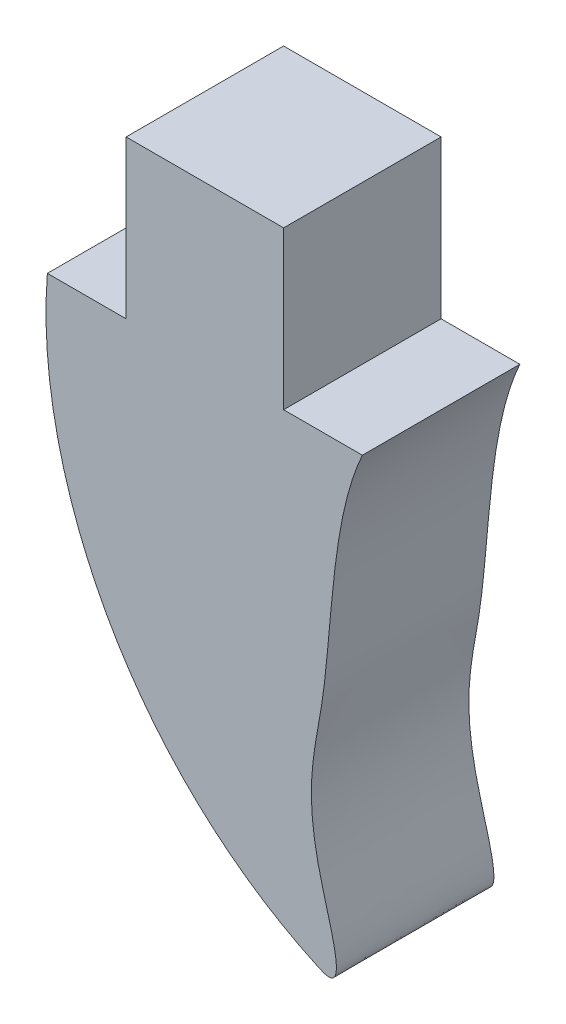
SolidWorks part; units mm, degrees
ref_plane "Front Plane" through (0, 0, 0) normal (0, 0, 1) x (1, 0, 0)
ref_plane "Top Plane" through (0, 0, 0) normal (0, 1, 0) x (1, 0, 0)
ref_plane "Right Plane" through (0, 0, 0) normal (1, 0, 0) x (0, 0, -1)
sketch "Sketch1" plane through (0, 0, 0) normal (0, 0, 1) x (1, 0, 0)
  line L0 (-3.175, -1.5875) -> (3.175, -1.5875)
  line L1 (1.5875, -1.5875) -> (-1.5875, -1.5875)
  line L2 (1.5875, -1.5875) -> (1.5875, 1.5875)
  line L3 (1.5875, 1.5875) -> (-1.5875, 1.5875)
  line L4 (-1.5875, -1.5875) -> (-1.5875, 1.5875)
  line L5 (1.5875, -1.5875) -> (-1.5875, 1.5875) construction
  line L6 (1.5875, 1.5875) -> (-1.5875, -1.5875) construction
  spline S0 degree 3 poles (-3.175, -1.5875) (-3.4659, -5.2784) (-1.3649, -9.3223) (2.938, -11.2635) (1.8454, -8.3286) (2.6075, -6.0833) (2.5313, -3.0014) (3.175, -1.5875) knots 0 0 0 0 0.534256 0.543776 0.625265 0.768464 1 1 1 1
  point P0 (0, 0)
  dimension "D1" = 3.175
  dimension "D2" = 3.175
  dimension "D3" = 1.5875
  dimension "D4" = 1.5875
extrude "Boss-Extrude1" add sketch "Sketch1" along normal blind 3.175 contours L0 S0 | L4 L0 L2 L3
